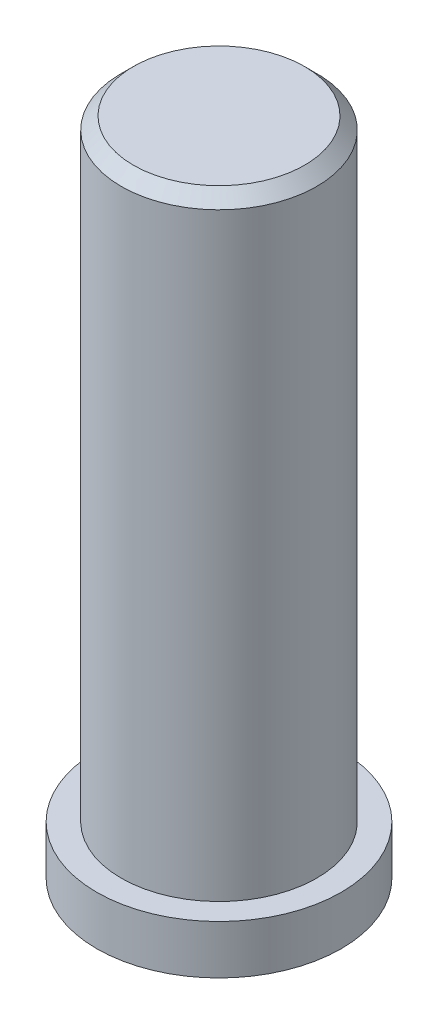
SolidWorks part; units mm, degrees
ref_plane "Front Plane" through (0, 0, 0) normal (0, 0, 1) x (1, 0, 0)
ref_plane "Top Plane" through (0, 0, 0) normal (0, 1, 0) x (1, 0, 0)
ref_plane "Right Plane" through (0, 0, 0) normal (1, 0, 0) x (0, 0, -1)
sketch "Sketch1" plane through (0, 0, 0) normal (0, 1, 0) x (1, 0, 0)
  circle A0 centre (0, 0) radius 5
  dimension "D1" = 10
extrude "Boss-Extrude1" add sketch "Sketch1" along normal blind 2
sketch "Sketch2" plane through (0, 2, 0) normal (0, 1, 0) x (1, 0, 0)
  circle A0 centre (0, 0) radius 4
  dimension "D1" = 8
extrude "Boss-Extrude2" add sketch "Sketch2" along normal blind 25
chamfer "Chamfer1" distance 0.5 angle 45 1 edges at (0, 27, 4)
